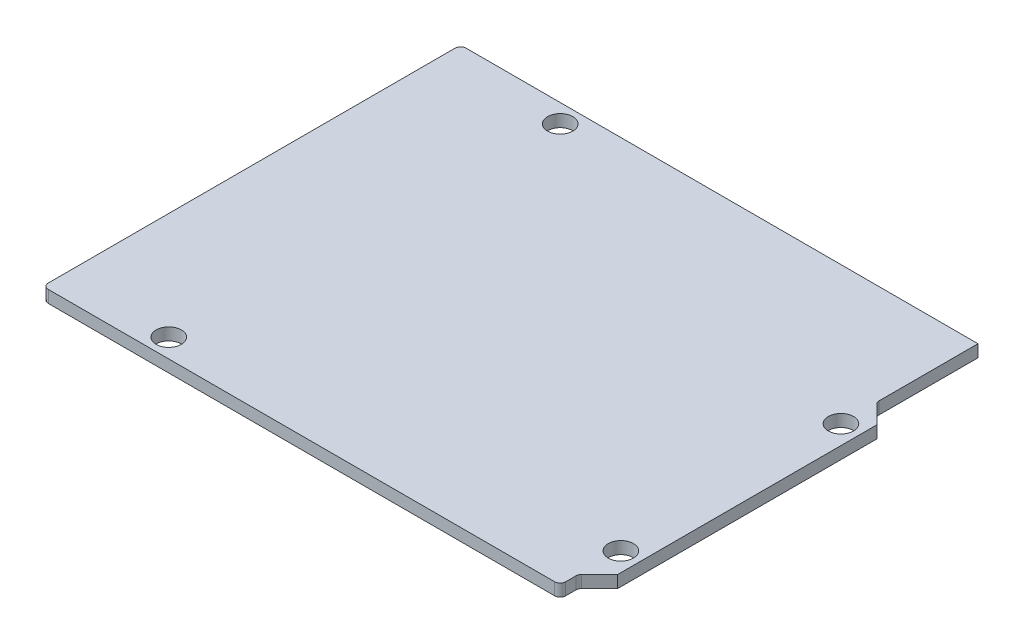
SolidWorks part; units mm, degrees
ref_plane "Plan de face" through (0, 0, 0) normal (0, 0, 1) x (1, 0, 0)
ref_plane "Plan de dessus" through (0, 0, 0) normal (0, 1, 0) x (1, 0, 0)
ref_plane "Plan de droite" through (0, 0, 0) normal (1, 0, 0) x (0, 0, -1)
sketch "Esquisse1" plane through (0, 0, 0) normal (0, 1, 0) x (1, 0, 0)
  line L0 (65.7, 53.05) -> (65.7, 40.2)
  line L1 (0, 0) -> (65.7, 0)
  line L2 (0, 0) -> (0, 53.05)
  line L3 (0, 53.05) -> (65.7, 53.05)
  line L4 (68.2, 4.8) -> (68.2, 37.7)
  line L5 (65.7, 40.2) -> (68.2, 37.7)
  line L6 (68.2, 4.8) -> (65.7, 2.3)
  line L7 (65.7, 2.3) -> (65.7, 0)
  circle A0 centre (15, 50.7) radius 1.6
  circle A1 centre (13.6, 2.4) radius 1.6
  circle A2 centre (65.8, 7.6) radius 1.6
  circle A3 centre (65.8, 35.55) radius 1.6
  dimension "D8" = 3.2
  dimension "D9" = 3.2
  dimension "D10" = 3.2
  dimension "D11" = 3.2
  dimension "D12" = 2.4
  dimension "D13" = 27.95
  dimension "D14" = 7.6
  dimension "D15" = 2.4
  dimension "D16" = 15
  dimension "D17" = 2.35
  dimension "D18" = 2.4
  dimension "D19" = 13.6
  dimension "D1" = 53.05
  dimension "D2" = 68.2
  dimension "D3" = 2.5
  dimension "D4" = 135
  dimension "D5" = 135
  dimension "D6" = 32.9
  dimension "D7" = 2.3
extrude "Boss.-Extru.1" add sketch "Esquisse1" along normal blind 1.55
fillet "Congé1" radius 0.7 5 edges at (65.7, 0.775, -40.2) (65.7, 0.775, -2.3) (65.7, 0.775, 0) (0, 0.775, -53.05) (0, 0.775, 0)
